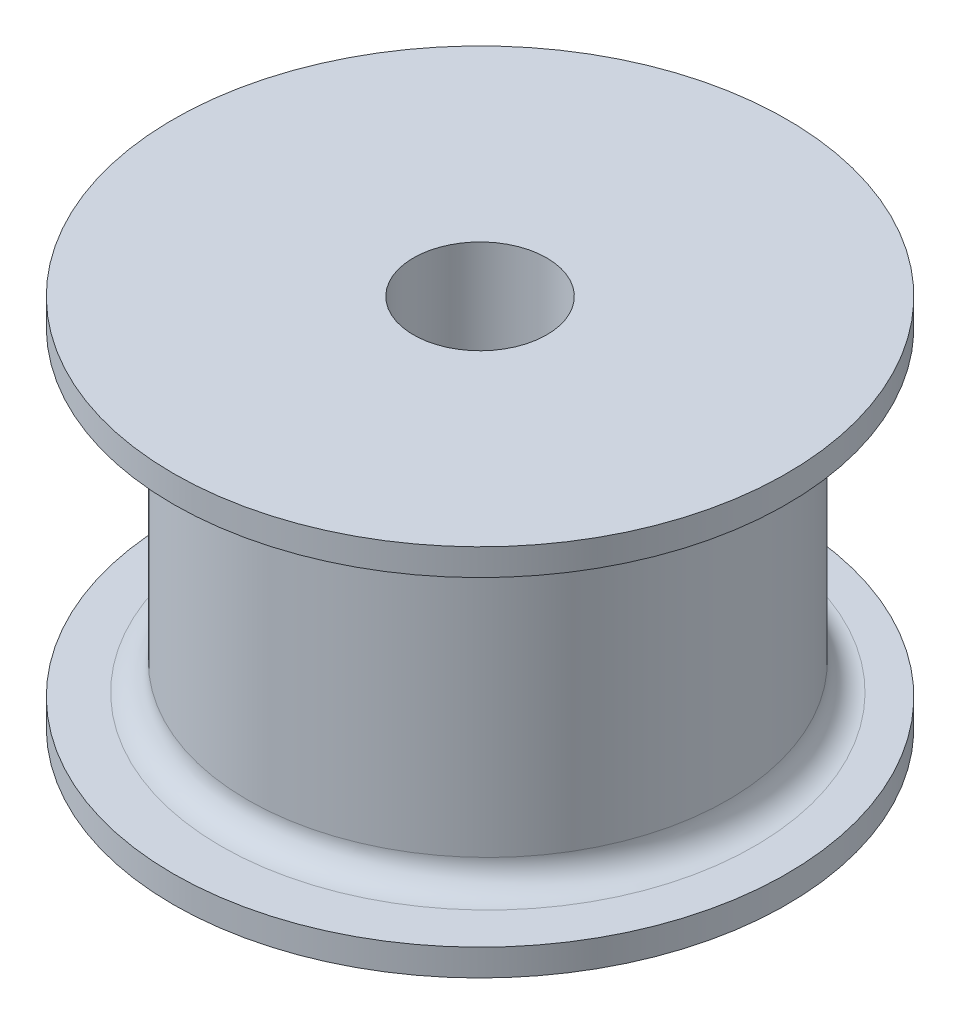
SolidWorks part; units mm, degrees
ref_plane "Front Plane" through (0, 0, 0) normal (0, 0, 1) x (1, 0, 0)
ref_plane "Top Plane" through (0, 0, 0) normal (0, 1, 0) x (1, 0, 0)
ref_plane "Right Plane" through (0, 0, 0) normal (1, 0, 0) x (0, 0, -1)
sketch "Sketch1" plane through (0, 0, 0) normal (0, 1, 0) x (1, 0, 0)
  circle A0 centre (0, 0) radius 4.95
extrude "Boss-Extrude2" add sketch "Sketch1" along normal blind 0.001 contours A0
sketch "Sketch4" plane through (0, 0.001, 0) normal (0, 1, 0) x (1, 0, 0)
  circle A0 centre (0, 0) radius 11.5
extrude "Boss-Extrude3" add sketch "Sketch4" along normal blind 1
sketch "Sketch5" plane through (0, 1.001, 0) normal (0, 1, 0) x (1, 0, 0)
  circle A0 centre (0, 0.2911) radius 9
extrude "Boss-Extrude4" add sketch "Sketch5" along normal blind 12
sketch "Sketch6" plane through (0, 13.001, 0) normal (0, 1, 0) x (1, 0, 0)
  circle A0 centre (0, 0) radius 11.5
extrude "Boss-Extrude5" add sketch "Sketch6" along normal blind 1
fillet "Fillet1" radius 1 1 edges at (0, 1.001, 8.7089)
fillet "Fillet2" radius 1 1 edges at (0, 13.001, 8.7089)
sketch "Sketch7" plane through (0, 0, 0) normal (0, -1, 0) x (1, 0, 0)
  circle A0 centre (0, 0) radius 2.5
extrude "Cut-Extrude1" cut sketch "Sketch7" against normal through all
